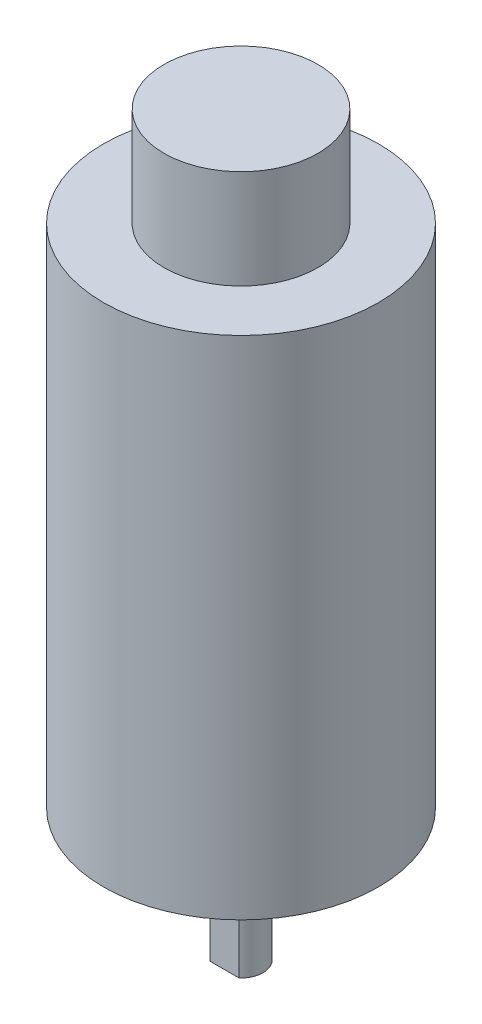
SolidWorks part; units mm, degrees
ref_plane "Front Plane" through (0, 0, 0) normal (0, 0, 1) x (1, 0, 0)
ref_plane "Top Plane" through (0, 0, 0) normal (0, 1, 0) x (1, 0, 0)
ref_plane "Right Plane" through (0, 0, 0) normal (1, 0, 0) x (0, 0, -1)
other "Configuration Table"
sketch "Sketch1" plane through (0, 0, 0) normal (0, 1, 0) x (1, 0, 0)
  line L0 (-1.3229, 1.5) -> (1.3229, 1.5)
  circle A0 centre (0, 0) radius 12.5
  circle A1 centre (0, 8.5) radius 1.5
  circle A2 centre (0, -8.5) radius 1.5
  circle A3 centre (0, 0) radius 3.5
  circle A5 centre (0, 0) radius 2
  point P10 (0, 0)
  point P11 (0, 0)
  point P12 (0, 0)
  point P13 (0, 0)
  point P14 (0, 0)
  point P15 (0, 0)
  point P17 (0, 0)
  point P18 (0, 0)
  dimension "D1" = 17
  dimension "D2" = 3
  dimension "D3" = 3
  dimension "D4" = 25
  dimension "D5" = 7
  dimension "D6" = 4
  dimension "D7" = 8.5
  dimension "D8" = 8.5
  dimension "D10" = 12.5
  dimension "D12" = 2.5
  dimension "D9" = 2.6458
extrude "Body" add sketch "Sketch1" along normal blind 46 contours A0
sketch "Sketch2" plane through (0, 46, 0) normal (0, 1, 0) x (1, 0, 0)
  circle A0 centre (0, 0) radius 7
extrude "Boss-Extrude4" add sketch "Sketch2" along normal blind 9
sketch "Sketch5" plane through (0, 0, 0) normal (0, 1, 0) x (1, 0, 0)
  line L0 (-1.3229, 1.5) -> (1.3229, 1.5) construction
  circle A0 centre (0, 0) radius 3.5
  circle A1 centre (0, 0) radius 2
extrude "Boss-Extrude5" add sketch "Sketch5" against normal blind 2.5
sketch "Sketch10" plane through (0, 0, 0) normal (0, 1, 0) x (1, 0, 0)
  circle A0 centre (0, 0) radius 2
extrude "Boss-Extrude6" add sketch "Sketch10" against normal blind 12
sketch "Sketch11" plane through (0, -12, 0) normal (0, -1, 0) x (1, 0, 0)
  line L2 (-1.3229, 1.5) -> (1.3229, 1.5)
  arc A0 (1.3229, 1.5) -> (-1.3229, 1.5) centre (0, 0) ccw
sketch "Sketch12" plane through (0, -12, 0) normal (0, -1, 0) x (1, 0, 0)
  line L0 (-1.3229, 1.5) -> (1.3229, 1.5)
  arc A0 (1.3229, 1.5) -> (-1.3229, 1.5) centre (0, 0) ccw
extrude "Cut-Extrude1" cut sketch "Sketch12" against normal blind 8
sketch "Sketch13" plane through (0, 0, 0) normal (0, 1, 0) x (1, 0, 0)
  circle A0 centre (0, 8.5) radius 1.5
  circle A1 centre (0, -8.5) radius 1.5
extrude "Cut-Extrude2" cut sketch "Sketch13" along normal blind 4
